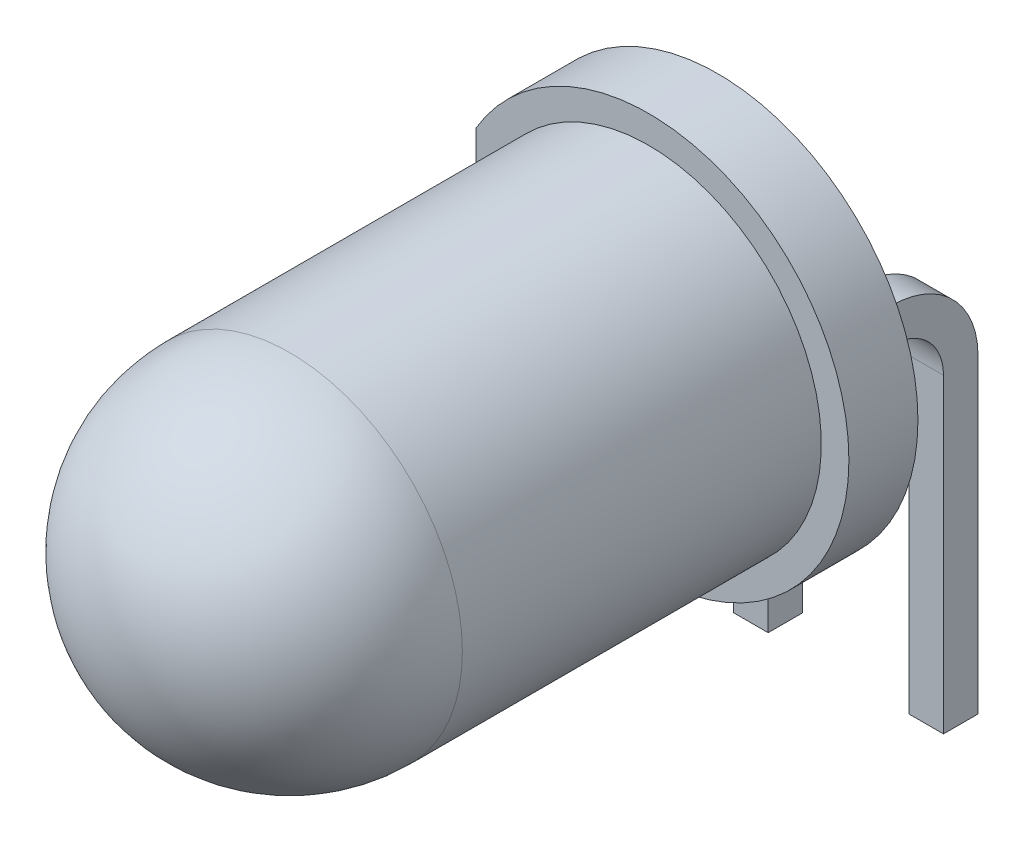
SolidWorks part; units mm, degrees
ref_plane "Plan de face" through (0, 0, 0) normal (0, 0, 1) x (1, 0, 0)
ref_plane "Plan de dessus" through (0, 0, 0) normal (0, 1, 0) x (1, 0, 0)
ref_plane "Plan de droite" through (0, 0, 0) normal (1, 0, 0) x (0, 0, -1)
sketch "Esquisse3" plane through (0, 0, 0) normal (0, 0, 1) x (1, 0, 0)
  circle A0 centre (0, 0) radius 2.9
  dimension "D1" = 5.8
extrude "Boss.-Extru.1" add sketch "Esquisse3" along normal blind 1
sketch "Esquisse5" plane through (0, 0, 0) normal (0, 1, 0) x (1, 0, 0)
  line L0 (0, -1) -> (0, -8.7)
  line L1 (2.5, -6.2) -> (2.5, -1)
  line L2 (2.5, -1) -> (0, -1)
  line L4 (-2.9, -1) -> (2.9, -1) construction
  arc A0 (2.5, -6.2) -> (0, -8.7) centre (0, -6.2) cw
  dimension "D3" = 2.5
  dimension "D1" = 2.5
  dimension "D2" = 7.7
revolve "Révolution1" add sketch "Esquisse5" angle 360 about L0
sketch "Esquisse6" plane through (0, 0, 1) normal (0, 0, 1) x (1, 0, 0)
  line L0 (-2.5, 1.4697) -> (-2.5, -1.4697)
  circle A0 centre (0, 0) radius 2.9 construction
  circle A1 centre (0, 0) radius 2.5 construction
  point P4 (-2.5, 0)
extrude "Enlèv. mat.-Extru.1" cut sketch "Esquisse6" against normal through all and the other way through all flip side to cut
sketch "Esquisse7" plane through (0, 0, 0) normal (0, 0, 1) x (1, 0, 0)
  line L0 (2.9, 0) -> (-2.5, 0) construction
  line L1 (1.52, 0.25) -> (1.02, 0.25)
  line L2 (1.52, 0.25) -> (1.52, -0.25)
  line L3 (1.52, -0.25) -> (1.02, -0.25)
  line L4 (1.02, 0.25) -> (1.02, -0.25)
  line L5 (-1.02, 0.25) -> (-1.52, 0.25)
  line L6 (-1.02, 0.25) -> (-1.02, -0.25)
  line L7 (-1.02, -0.25) -> (-1.52, -0.25)
  line L8 (-1.52, 0.25) -> (-1.52, -0.25)
  line L9 (-2.5, -1.4697) -> (-2.5, 1.4697) construction
  line L10 (1.02, 0.25) -> (-1.02, 0.25) construction
  line L11 (-1.02, -0.25) -> (1.02, -0.25) construction
  line L12 (0, 0.25) -> (0, -0.25) construction
  arc A0 (-2.5, -1.4697) -> (-2.5, 1.4697) centre (0, 0) ccw construction
  point P17 (1.27, -0.25)
  point P18 (-1.27, -0.25)
  dimension "D1" = 0.5
  dimension "D2" = 0.5
  dimension "D3" = 0.5
  dimension "D4" = 2.54
sketch "Esquisse8" plane through (0, 0, 0) normal (1, 0, 0) x (0, 0, -1)
  line L0 (0, 0) -> (1, 0)
  line L1 (2, -1) -> (2, -5.5)
  arc A0 (1, 0) -> (2, -1) centre (1, -1) cw
  point P8 (0.6601, 0)
  dimension "D2" = 1
  dimension "D1" = 1
  dimension "D3" = 5.5
sweep "Balayage1" add profiles "Esquisse7" path "Esquisse8"
